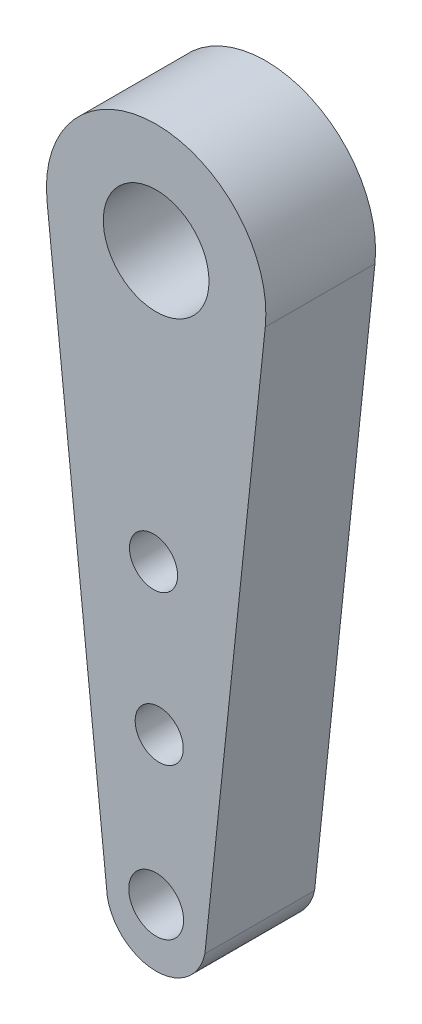
SolidWorks part; units mm, degrees
material "ABS"
ref_plane "Front Plane" through (0, 0, 0) normal (0, 0, 1) x (1, 0, 0)
ref_plane "Top Plane" through (0, 0, 0) normal (0, 1, 0) x (1, 0, 0)
ref_plane "Right Plane" through (0, 0, 0) normal (1, 0, 0) x (0, 0, -1)
sketch "Sketch1" plane through (0, 0, 0) normal (0, 0, 1) x (1, 0, 0)
  line L0 (4.3302, 6.2631) -> (2.6797, -9.4033)
  line L1 (-2.0853, 9.5774) -> (4.8151, 9.5774)
  line L2 (-2.0853, 9.5774) -> (-2.0853, -10.4226)
  line L4 (4.8151, 9.5774) -> (4.8151, -10.4226)
  line L5 (-1.6367, 6.2631) -> (0.0137, -9.4033)
  arc A1 (4.3302, 6.2631) -> (-1.6367, 6.2631) centre (1.3467, 6.5774) ccw
  arc A3 (2.7097, -9.1192) -> (-0.0162, -9.1192) centre (1.3467, -9.1192) cw
  arc A4 (-2.0853, -10.4226) -> (4.8151, -10.4226) centre (1.3649, -10.4226) ccw
  circle A5 centre (1.3467, 6.5774) radius 1.4453
  dimension "D1" = 20
  dimension "D2" = 6
extrude "Boss-Extrude1" add sketch "Sketch1" along normal blind 3 contours A3 L0 A1 L5 A5
sketch "Sketch2" plane through (0, 0, 3) normal (0, 0, 1) x (1, 0, 0)
  circle A0 centre (1.3467, -8.9031) radius 0.75
  dimension "D1" = 1.5
extrude "Cut-Extrude1" cut sketch "Sketch2" against normal blind 10
sketch "Sketch3" plane through (0, 0, 0) normal (0, 0, -1) x (-1, 0, 0)
  circle A2 centre (-1.2754, -0.82) radius 0.6577
extrude "Cut-Extrude2" cut sketch "Sketch3" against normal through all
sketch "Sketch4" plane through (0, 0, 0) normal (0, 0, -1) x (-1, 0, 0)
  circle A0 centre (-1.4306, -4.8372) radius 0.6577
  circle A1 centre (-1.2754, -0.82) radius 0.6577 construction
extrude "Cut-Extrude3" cut sketch "Sketch4" against normal through all
